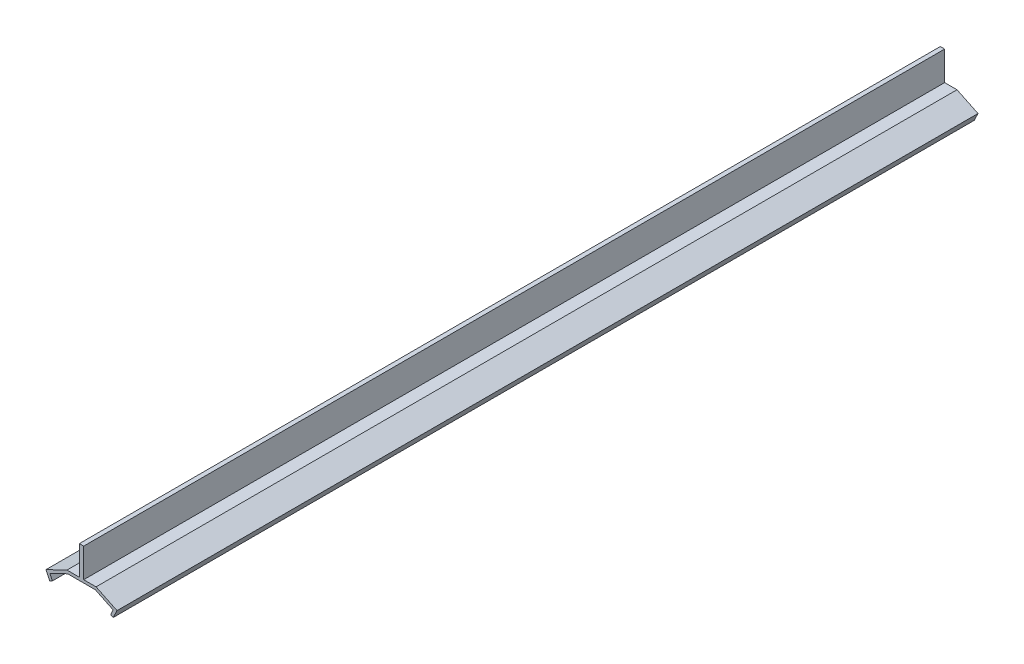
SolidWorks part; units mm, degrees
material "PA 6/6 polyamide Type 6-6 (Nylon)"
ref_plane "Plan de face" through (0, 0, 0) normal (0, 0, 1) x (1, 0, 0)
ref_plane "Plan de dessus" through (0, 0, 0) normal (0, 1, 0) x (1, 0, 0)
ref_plane "Plan de droite" through (0, 0, 0) normal (1, 0, 0) x (0, 0, -1)
sketch "Esquisse1" plane through (0, 0, 0) normal (0, 0, 1) x (1, 0, 0)
  line L0 (-5, 0) -> (5, 0) construction
  line L1 (-5, 0) -> (-182.5, -85.5) construction
  line L2 (-182.5, -85.5) -> (182.5, -85.5) construction
  line L3 (0, 0) -> (0, -1) construction
  line L4 (0, -85.5) -> (0, -1) construction
  line L5 (-0.75, 0) -> (-0.75, 10)
  line L6 (-0.75, 10) -> (0.75, 10)
  line L7 (0.75, 10) -> (0.75, 0)
  line L8 (0, 10) -> (0, 0) construction
  line L9 (5, 0) -> (182.5, -85.5) construction
  line L10 (-5, 0) -> (-12.2074, -3.4717)
  line L11 (-12.2074, -3.4717) -> (-10.9055, -6.1745)
  line L12 (-10.8725, -3.9387) -> (-4.7717, -1)
  line L13 (-4.7717, -1) -> (4.7717, -1)
  line L14 (4.7717, -1) -> (10.8725, -3.9387)
  line L15 (10.9055, -6.1745) -> (12.2074, -3.4717)
  line L16 (12.2074, -3.4717) -> (5, 0)
  line L17 (5, 0) -> (0.75, 0)
  line L18 (-0.75, 0) -> (-5, 0)
  line L19 (-10.8725, -3.9387) -> (-10.0046, -5.7406)
  line L20 (-10.0046, -5.7406) -> (-10.9055, -6.1745)
  line L21 (10.8725, -3.9387) -> (10.0046, -5.7406)
  line L22 (10.0046, -5.7406) -> (10.9055, -6.1745)
  point P15 (0, 0)
  dimension "D1" = 365
  dimension "D2" = 85.5
  dimension "D3" = 10
  dimension "D4" = 10
  dimension "D5" = 1
  dimension "D6" = 8
  dimension "D7" = 1
  dimension "D8" = 1.5
  dimension "D9" = 1
  dimension "D10" = 3
extrude "Extrusion1" add sketch "Esquisse1" along normal mid plane 296
